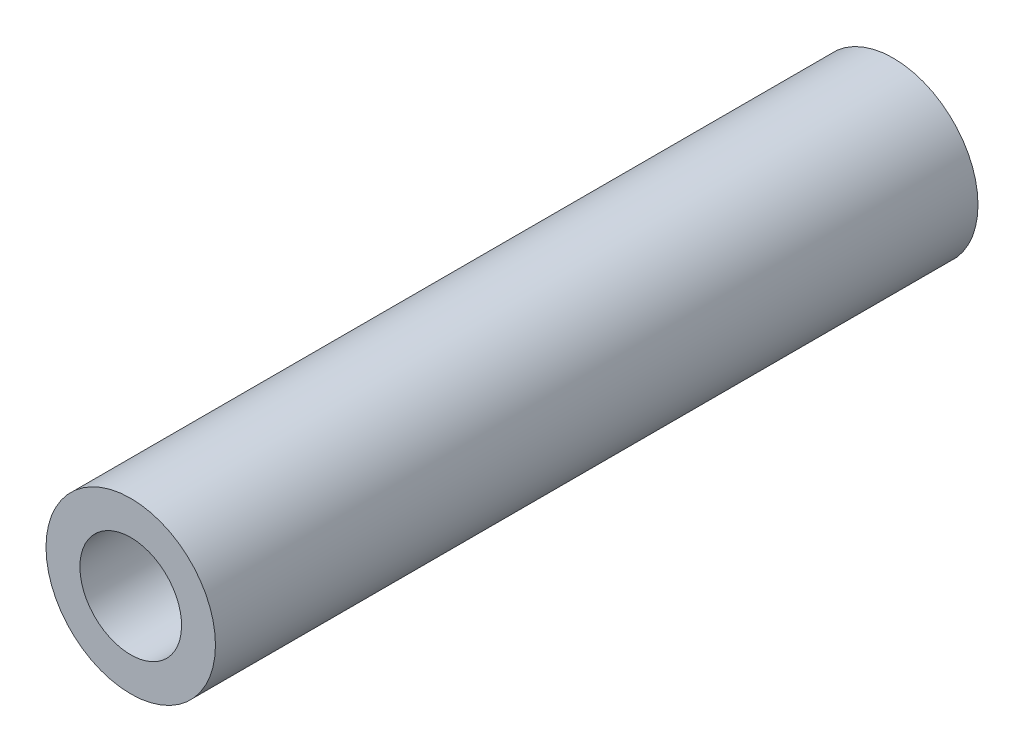
SolidWorks part; units mm, degrees
material "Plain Carbon Steel"
ref_plane "Front Plane" through (0, 0, 0) normal (0, 0, 1) x (1, 0, 0)
ref_plane "Top Plane" through (0, 0, 0) normal (0, 1, 0) x (1, 0, 0)
ref_plane "Right Plane" through (0, 0, 0) normal (1, 0, 0) x (0, 0, -1)
sketch "Sketch1" plane through (0, 0, 0) normal (1, 0, 0) x (0, 0, -1)
  line L0 (10, 0) -> (10, 3)
  line L1 (10, 3) -> (0, 3)
  line L2 (0, 3) -> (0, 5)
  line L3 (0, 5) -> (45, 5)
  line L4 (45, 5) -> (45, 3)
  line L5 (45, 3) -> (35, 3)
  line L6 (35, 3) -> (35, 0)
  line L7 (35, 0) -> (10, 0)
  dimension "D1" = 45
  dimension "D2" = 5
  dimension "D3" = 3
  dimension "D4" = 10
revolve "Revolve1" add sketch "Sketch1" angle 360 about L7
